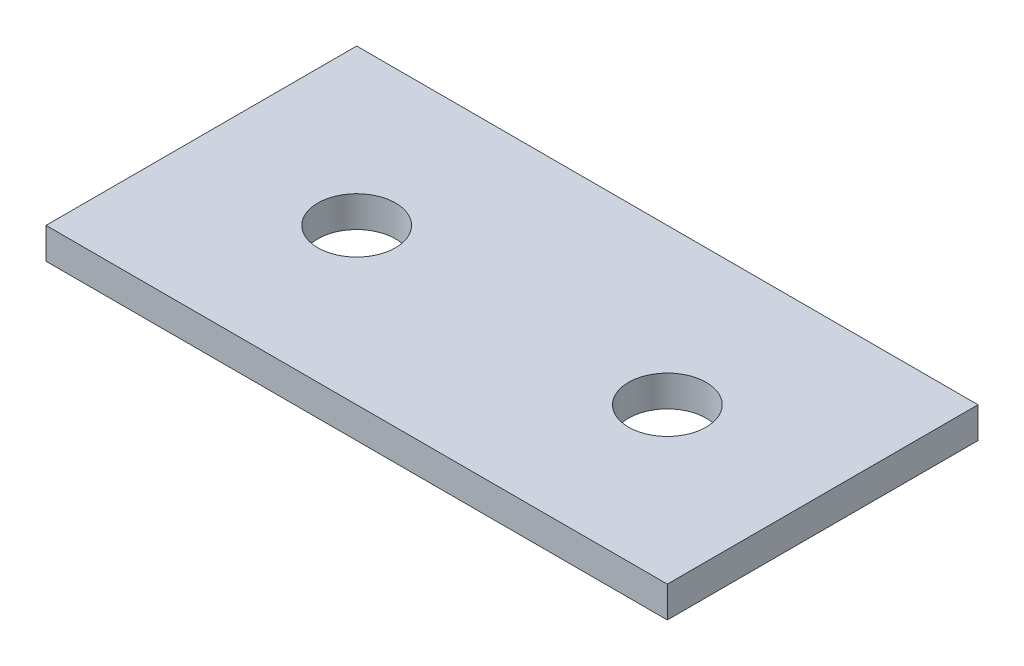
SolidWorks part; units mm, degrees
ref_plane "Front Plane" through (0, 0, 0) normal (0, 0, 1) x (1, 0, 0)
ref_plane "Top Plane" through (0, 0, 0) normal (0, 1, 0) x (1, 0, 0)
ref_plane "Right Plane" through (0, 0, 0) normal (1, 0, 0) x (0, 0, -1)
sketch "Sketch1" plane through (0, 0, 0) normal (0, 1, 0) x (1, 0, 0)
  line L1 (-50.8, 25.4) -> (0, 25.4)
  line L2 (-50.8, 25.4) -> (-50.8, 0)
  line L3 (-50.8, 0) -> (0, 0)
  line L4 (0, 25.4) -> (0, 0)
  circle A0 centre (-38.1, 12.7) radius 3.175
  circle A1 centre (-12.7, 12.7) radius 3.175
  dimension "D3" = 6.35
  dimension "D4" = 6.35
  dimension "D1" = 50.8
  dimension "D2" = 25.4
  dimension "D5" = 25.4
  dimension "D6" = 12.7
  dimension "D7" = 12.7
extrude "Boss-Extrude1" add sketch "Sketch1" along normal blind 2.54
